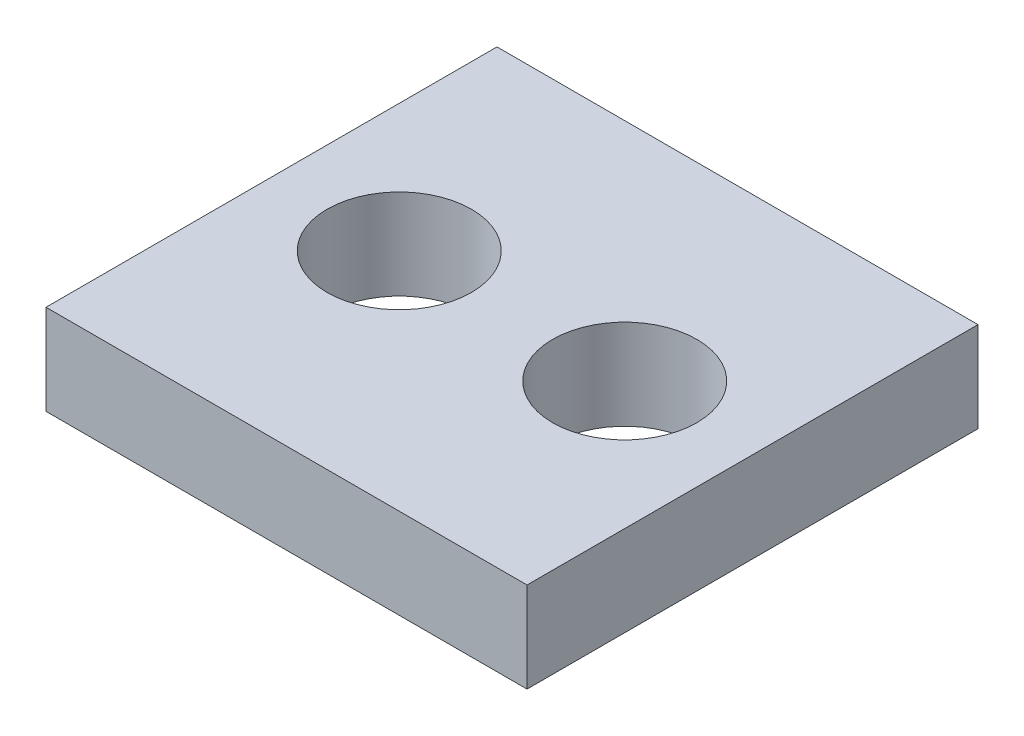
SolidWorks part; units mm, degrees
ref_plane "Front Plane" through (0, 0, 0) normal (0, 0, 1) x (1, 0, 0)
ref_plane "Top Plane" through (0, 0, 0) normal (0, 1, 0) x (1, 0, 0)
ref_plane "Right Plane" through (0, 0, 0) normal (1, 0, 0) x (0, 0, -1)
sketch "Sketch1" plane through (0, 0, 0) normal (0, 1, 0) x (1, 0, 0)
  line L1 (-8, -7.5) -> (8, -7.5)
  line L2 (-8, -7.5) -> (-8, 7.5)
  line L3 (-8, 7.5) -> (8, 7.5)
  line L4 (8, -7.5) -> (8, 7.5)
  line L5 (-8, -7.5) -> (8, 7.5) construction
  line L6 (-8, 7.5) -> (8, -7.5) construction
  point P0 (0, 0)
  dimension "D1" = 16
  dimension "D2" = 15
extrude "Boss-Extrude1" add sketch "Sketch1" along normal blind 3
sketch "Sketch2" plane through (0, 3, 0) normal (0, 1, 0) x (1, 0, 0)
  circle A0 centre (-3.75, 0) radius 2.4
  dimension "D2" = 4.8
  dimension "D1" = 3.75
extrude "Cut-Extrude1" cut sketch "Sketch2" against normal through all both and the other way through all
mirror "Mirror1" about plane through (0, 0, 0) normal (1, 0, 0) of "Cut-Extrude1"
